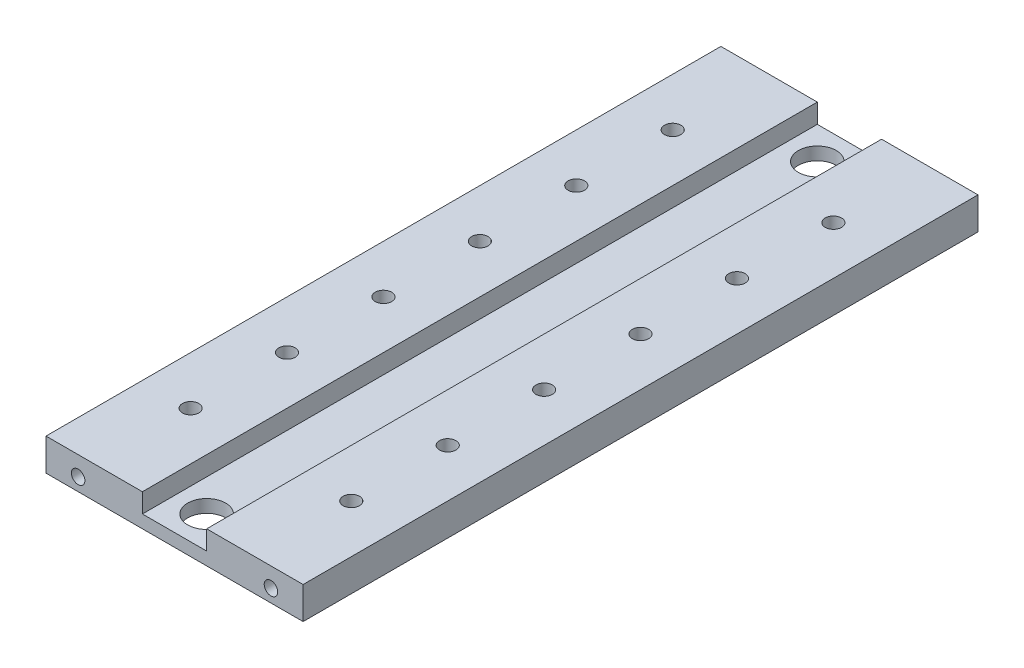
SolidWorks part; units mm, degrees
material "ABS PC"
ref_plane "Ebene vorne" through (0, 0, 0) normal (0, 0, 1) x (1, 0, 0)
ref_plane "Ebene oben" through (0, 0, 0) normal (0, 1, 0) x (1, 0, 0)
ref_plane "Ebene rechts" through (0, 0, 0) normal (1, 0, 0) x (0, 0, -1)
sketch "Skizze1" plane through (0, 0, 0) normal (0, 0, 1) x (1, 0, 0)
  line L0 (-40, 0) -> (40, 0)
  line L1 (40, 0) -> (40, 10)
  line L2 (40, 10) -> (10, 10)
  line L3 (10, 10) -> (10, 4)
  line L4 (10, 4) -> (-10, 4)
  line L5 (-10, 4) -> (-10, 10)
  line L6 (-10, 10) -> (-40, 10)
  line L7 (-40, 10) -> (-40, 0)
  point P3 (0, 0)
  point P10 (0, 4)
  dimension "D1" = 10
  dimension "D2" = 80
  dimension "D3" = 20
  dimension "D4" = 4
extrude "Aufsatz-Linear austragen1" add sketch "Skizze1" along normal mid plane 210
sketch "Skizze3" plane through (0, 0, 0) normal (0, 0, 1) x (1, 0, 0)
  line L0 (-40, 0) -> (40, 0) construction
  line L1 (0, 0) -> (0, 4) construction
  line L2 (10, 4) -> (-10, 4) construction
  point P0 (-25, 4)
  point P1 (25, 4)
  dimension "D1" = 50
  dimension "D2" = 4
hole_wizard "M5 Gewindebohrung1" positions "Skizze5" profile "Skizze6" tap size "M5" standard "DIN"
sketch "Skizze5" plane through (0, 0, 105) normal (0, 0, 1) x (1, 0, 0)
  line L0 (0, 0) -> (0, 10) construction
  line L1 (-40, 0) -> (40, 0) construction
  line L3 (40, 10) -> (10, 10) construction
  point P0 (-30, 4)
  point P3 (30, 4)
  dimension "D1" = 60
  dimension "D2" = 4
sketch "Skizze6" plane through (-30, 4, 105) normal (1, 0, 0) x (0, -1, 0)
  line L0 (0, 0) -> (0, 15.2618)
  line L1 (0, 15.2618) -> (2.1, 14)
  line L2 (2.1, 14) -> (2.1, 0)
  line L5 (2.1, 0) -> (0, 0)
  line L10 (0, 15.2618) -> (-2.1, 14) construction
  line L11 (0, -6.35) -> (0, 107.95) construction
  dimension "Bohrerdurchmesser" = 4.2
  dimension "Bohrungstiefe" = 14
  dimension "Spitzenwinkel" = 118
cosmetic thread "Bohrungsgewinde1" parameters "D1"=10, "D2"=5
cosmetic thread "Bohrungsgewinde2" parameters "D1"=10, "D2"=5
hole_wizard "M5 Gewindebohrung2" positions "Skizze8" profile "Skizze9" tap size "M5" standard "DIN"
sketch "Skizze8" plane through (0, 0, -105) normal (0, 0, -1) x (-1, 0, 0)
  point P0 (-25, 4)
  point P3 (25, 4)
sketch "Skizze9" plane through (25, 4, -105) normal (1, 0, 0) x (0, 1, 0)
  line L0 (0, 0) -> (0, 15.2618)
  line L1 (0, 15.2618) -> (2.1, 14)
  line L2 (2.1, 14) -> (2.1, 0)
  line L5 (2.1, 0) -> (0, 0)
  line L10 (0, 15.2618) -> (-2.1, 14) construction
  line L11 (0, -6.35) -> (0, 107.95) construction
  dimension "Bohrerdurchmesser" = 4.2
  dimension "Bohrungstiefe" = 14
  dimension "Spitzenwinkel" = 118
cosmetic thread "Bohrungsgewinde3" parameters "D1"=10, "D2"=5
cosmetic thread "Bohrungsgewinde4" parameters "D1"=10, "D2"=5
sketch "Skizze10" plane through (0, 10, 0) normal (0, 1, 0) x (1, 0, 0)
  line L0 (-40, 0) -> (40, 0) construction
  line L1 (-40, -105) -> (-40, 105) construction
  line L2 (40, -105) -> (40, 105) construction
  line L3 (25, 105) -> (25, -105) construction
  line L4 (40, 105) -> (10, 105) construction
  line L5 (40, -105) -> (10, -105) construction
  line L6 (0, 105) -> (0, -105) construction
  line L7 (10, 105) -> (-10, 105) construction
  line L8 (10, -105) -> (-10, -105) construction
  circle A0 centre (25, 75) radius 2.55
  circle A1 centre (25, 45) radius 2.55
  circle A2 centre (25, 15) radius 2.55
  circle A3 centre (25, -15) radius 2.55
  circle A4 centre (25, -45) radius 2.55
  circle A5 centre (25, -75) radius 2.55
  circle A6 centre (-25, -75) radius 2.55
  circle A7 centre (-25, -45) radius 2.55
  circle A8 centre (-25, -15) radius 2.55
  circle A9 centre (-25, 15) radius 2.55
  circle A10 centre (-25, 45) radius 2.55
  circle A11 centre (-25, 75) radius 2.55
  dimension "D2" = 30
  dimension "D3" = 30
  dimension "D4" = 5.1
  dimension "D1" = 30
extrude "Schnitt-Linear austragen1" cut sketch "Skizze10" against normal through all
hole_wizard "G1/4 Gewindebohrung1" positions "Skizze13" profile "Skizze12" tap size "G1/4" standard "GB" end condition through all
sketch "Skizze13" plane through (0, 4, 0) normal (0, 1, 0) x (1, 0, 0)
  line L0 (10, 105) -> (-10, 105) construction
  line L1 (-40, -105) -> (40, -105) construction
  point P0 (0, 95)
  point P5 (0, 105)
  point P6 (0, -95)
  dimension "D1" = 10
  dimension "D2" = 10
sketch "Skizze12" plane through (0, 4, -95) normal (1, 0, 0) x (0, 0, 1)
  line L0 (0, 0) -> (0, 4)
  line L1 (0, 4) -> (5.9, 4)
  line L2 (5.9, 4) -> (5.9, 0)
  line L5 (5.9, 0) -> (0, 0)
  line L11 (0, -6.35) -> (0, 107.95) construction
  dimension "Bohrerdurchmesser" = 11.8
  dimension "Bohrungstiefe" = 4
cosmetic thread "Bohrungsgewinde5" parameters "D2"=13.157
cosmetic thread "Bohrungsgewinde6" parameters "D2"=13.157
